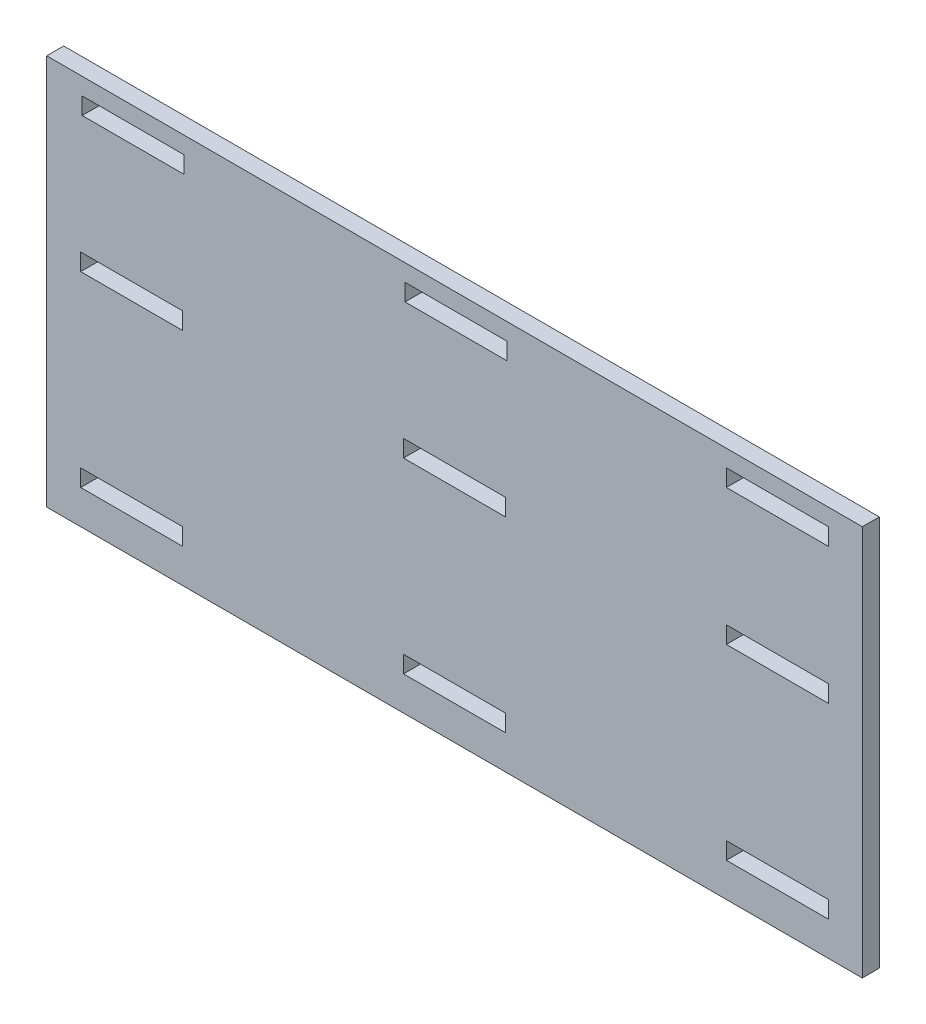
SolidWorks part; units mm, degrees
ref_plane "Front Plane" through (0, 0, 0) normal (0, 0, 1) x (1, 0, 0)
ref_plane "Top Plane" through (0, 0, 0) normal (0, 1, 0) x (1, 0, 0)
ref_plane "Right Plane" through (0, 0, 0) normal (1, 0, 0) x (0, 0, -1)
sketch "Sketch2" plane through (0, 0, 0) normal (0, 0, 1) x (1, 0, 0)
  line L0 (-120, 52.5) -> (120, 52.5) construction
  line L1 (-120, 57.5) -> (120, 57.5)
  line L2 (-120, 57.5) -> (-120, -57.5)
  line L3 (-120, -57.5) -> (120, -57.5)
  line L4 (120, 57.5) -> (120, -57.5)
  line L5 (-120, 57.5) -> (120, -57.5) construction
  line L6 (-120, -57.5) -> (120, 57.5) construction
  line L7 (-120, 12.5) -> (120, 12.5) construction
  line L8 (-120, -42.5) -> (120, -42.5) construction
  line L10 (-109.5652, 52.5) -> (-79.5652, 52.5)
  line L11 (-109.5652, 52.5) -> (-109.5652, 47.5)
  line L12 (-109.5652, 47.5) -> (-79.5652, 47.5)
  line L13 (-79.5652, 52.5) -> (-79.5652, 47.5)
  line L14 (-14.5652, 52.5) -> (15.4348, 52.5)
  line L15 (-14.5652, 52.5) -> (-14.5652, 47.5)
  line L16 (-14.5652, 47.5) -> (15.4348, 47.5)
  line L17 (15.4348, 52.5) -> (15.4348, 47.5)
  line L18 (80, 52.5) -> (110, 52.5)
  line L19 (80, 52.5) -> (80, 47.5)
  line L20 (80, 47.5) -> (110, 47.5)
  line L21 (110, 52.5) -> (110, 47.5)
  line L22 (-110, 12.5) -> (-80, 12.5)
  line L23 (-110, 12.5) -> (-110, 7.5)
  line L24 (-110, 7.5) -> (-80, 7.5)
  line L25 (-80, 12.5) -> (-80, 7.5)
  line L26 (-15, 12.5) -> (15, 12.5)
  line L27 (-15, 12.5) -> (-15, 7.5)
  line L28 (-15, 7.5) -> (15, 7.5)
  line L29 (15, 12.5) -> (15, 7.5)
  line L30 (80, 12.5) -> (110, 12.5)
  line L31 (80, 12.5) -> (80, 7.5)
  line L32 (80, 7.5) -> (110, 7.5)
  line L33 (110, 12.5) -> (110, 7.5)
  line L34 (-110, -42.5) -> (-80, -42.5)
  line L35 (-110, -42.5) -> (-110, -47.5)
  line L36 (-110, -47.5) -> (-80, -47.5)
  line L37 (-80, -42.5) -> (-80, -47.5)
  line L38 (-15, -42.5) -> (15, -42.5)
  line L39 (-15, -42.5) -> (-15, -47.5)
  line L40 (-15, -47.5) -> (15, -47.5)
  line L41 (15, -42.5) -> (15, -47.5)
  line L46 (80, -42.5) -> (110, -42.5)
  line L47 (80, -42.5) -> (80, -47.5)
  line L48 (80, -47.5) -> (110, -47.5)
  line L49 (110, -42.5) -> (110, -47.5)
  point P0 (0, 0)
  point P48 (110, 50)
  point P49 (-79.5652, 50)
  point P50 (-15, -45)
  dimension "D1" = 240
  dimension "D2" = 115
  dimension "D3" = 5
  dimension "D4" = 10
  dimension "D5" = 30
  dimension "D6" = 30
  dimension "D7" = 30
  dimension "D8" = 30
  dimension "D9" = 30
  dimension "D10" = 30
  dimension "D11" = 30
  dimension "D12" = 30
  dimension "D13" = 30
  dimension "D14" = 5
  dimension "D15" = 5
  dimension "D16" = 5
  dimension "D17" = 5
  dimension "D18" = 5
  dimension "D19" = 5
  dimension "D20" = 5
  dimension "D21" = 5
  dimension "D22" = 5
  dimension "D23" = 40
  dimension "D24" = 55
  dimension "D25" = 65
  dimension "D26" = 10.4348
  dimension "D27" = 10
  dimension "D28" = 65
  dimension "D29" = 65
  dimension "D30" = 10
  dimension "D31" = 65
  dimension "D32" = 65
extrude "Boss-Extrude1" add sketch "Sketch2" along normal blind 5
